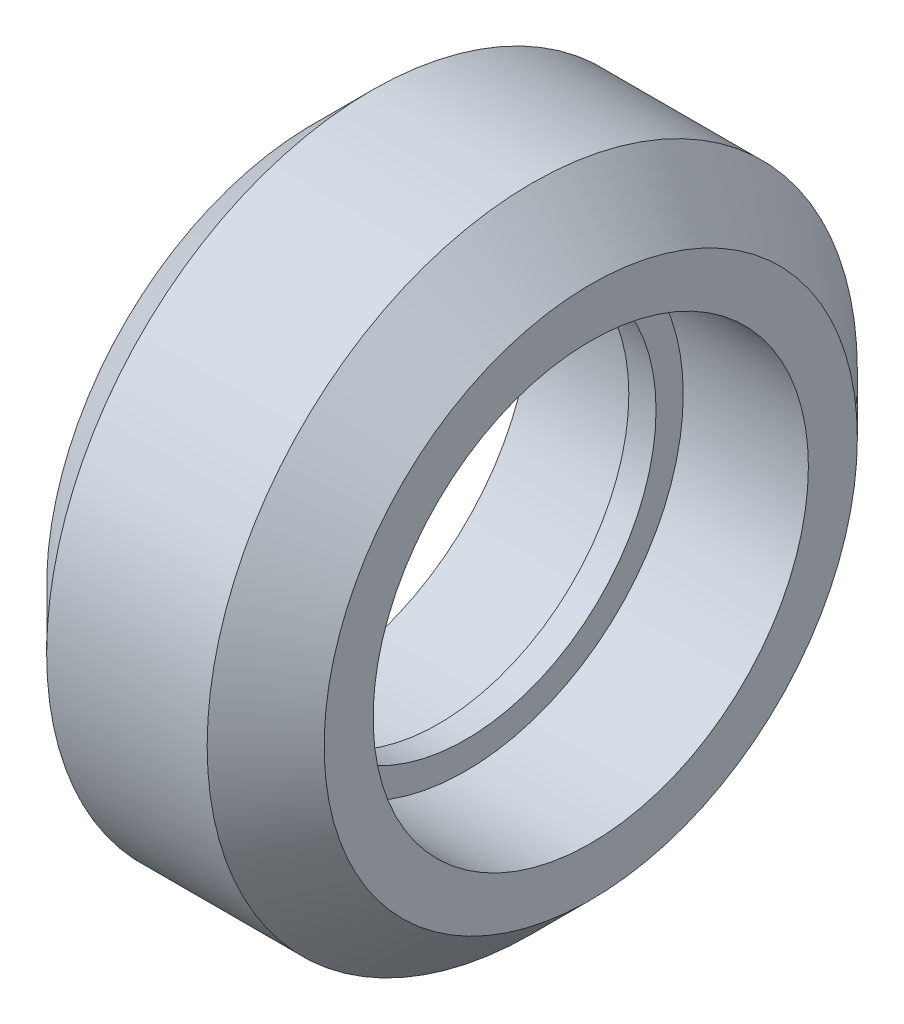
SolidWorks part; units mm, degrees
material "Delrin 2700 NC010, Low Viscosity Acetal Copolymer (SS)"
ref_plane "Front Plane" through (0, 0, 0) normal (0, 0, 1) x (1, 0, 0)
ref_plane "Top Plane" through (0, 0, 0) normal (0, 1, 0) x (1, 0, 0)
ref_plane "Right Plane" through (0, 0, 0) normal (1, 0, 0) x (0, 0, -1)
sketch "Sketch1" plane through (0, 0, 0) normal (0, 0, 1) x (1, 0, 0)
  line L0 (0.5, 7) -> (-0.5, 7)
  line L1 (-0.5, 7) -> (-0.5, 8)
  line L2 (-0.5, 8) -> (-5.1, 8)
  line L3 (-5.1, 8) -> (-5.1, 9.8)
  line L4 (-5.1, 9.8) -> (-2.95, 11.95)
  line L5 (-2.95, 11.95) -> (2.95, 11.95)
  line L6 (0, 11.95) -> (0, 7) construction
  line L7 (5.1, 9.8) -> (2.95, 11.95)
  line L8 (5.1, 8) -> (5.1, 9.8)
  line L9 (0.5, 8) -> (5.1, 8)
  line L10 (0.5, 7) -> (0.5, 8)
  line L11 (0, 0) -> (-12.6359, 0) construction
  dimension "D2" = 16
  dimension "D3" = 23.9
  dimension "D4" = 1
  dimension "D5" = 45
  dimension "D6" = 10.2
  dimension "D7" = 5.9
  dimension "D8" = 14
revolve "Revolve1" add sketch "Sketch1" angle 360 about L11
ref_plane "Plane1" through (0, 0, 0) normal (1, 0, 0) x (0, 0, -1)
